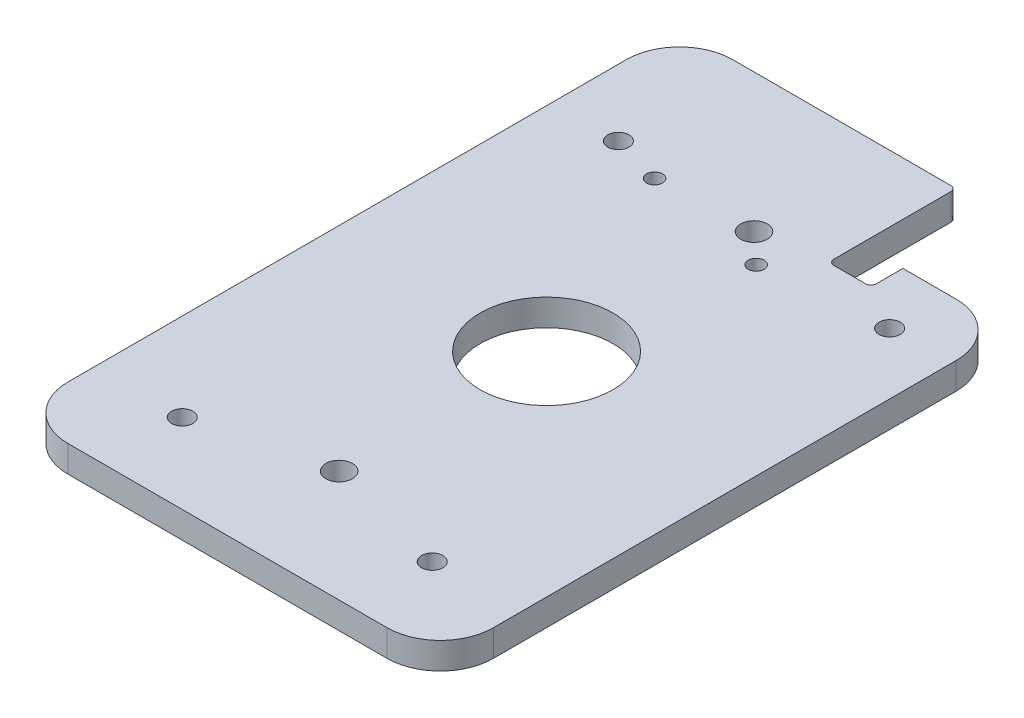
SolidWorks part; units mm, degrees
ref_plane "前视基准面" through (0, 0, 0) normal (0, 0, 1) x (1, 0, 0)
ref_plane "上视基准面" through (0, 0, 0) normal (0, 1, 0) x (1, 0, 0)
ref_plane "右视基准面" through (0, 0, 0) normal (1, 0, 0) x (0, 0, -1)
sketch "草图1" plane through (0, 0, 0) normal (0, 1, 0) x (1, 0, 0)
  line L0 (0, -49.286) -> (0, 59.6782) construction
  line L1 (-40, 65) -> (40, 65)
  line L2 (-40, 65) -> (-40, -60)
  line L3 (-40, -60) -> (40, -60)
  line L4 (40, 65) -> (40, -60)
  circle A0 centre (0, 0) radius 12.5
  dimension "D1" = 60
  dimension "D4" = 25
  dimension "D2" = 80
  dimension "D3" = 125
extrude "凸台-拉伸1" add sketch "草图1" along normal blind 5
sketch "草图2" plane through (0, 5, 0) normal (0, 1, 0) x (1, 0, 0)
  line L0 (40, 65) -> (-40, 65) construction
  line L1 (12, 65) -> (40, 65)
  line L2 (12, 65) -> (12, 47)
  line L3 (12, 47) -> (40, 47)
  line L4 (40, 65) -> (40, 47)
  line L5 (40, -60) -> (40, 65) construction
  dimension "D1" = 28
  dimension "D2" = 18
extrude "切除-拉伸1" cut sketch "草图2" against normal through all
hole_wizard "大小mm Clearance 暗销孔1" positions "草图3" profile "草图4" hole size "Ø4.0" standard "GB" end condition through all
sketch "草图3" plane through (0, 5, 0) normal (0, 1, 0) x (1, 0, 0)
  line L0 (0, -59.3844) -> (0, 58.2895) construction
  line L2 (30.3997, 0) -> (-33.5358, 0) construction
  point P0 (-23.5, -45)
  point P3 (23.5, -45)
  point P6 (28.5, 36)
  point P9 (-27.5, 41)
  dimension "D1" = 45
  dimension "D2" = 23.5
  dimension "D3" = 41
  dimension "D4" = 27.5
  dimension "D5" = 28.5
  dimension "D6" = 36
sketch "草图4" plane through (-23.5, 5, 45) normal (1, 0, 0) x (0, 0, 1)
  line L0 (0, 0) -> (0, 5)
  line L1 (0, 5) -> (2, 5)
  line L2 (2, 5) -> (2, 0)
  line L5 (2, 0) -> (0, 0)
  line L11 (0, -6.35) -> (0, 107.95) construction
  dimension "通孔孔直径" = 4
  dimension "通孔孔深度" = 5
hole_wizard "大小mm Transitional 暗销孔1" positions "草图5" profile "草图6" hole size "Ø5.0" standard "GB" end condition through all
sketch "草图5" plane through (0, 5, 0) normal (0, 1, 0) x (1, 0, 0)
  line L0 (28.4574, 0) -> (-29.0037, 0) construction
  line L1 (28.4574, 0) -> (-30.1367, 0) construction
  point P0 (0, -39)
  point P3 (0, 39)
  dimension "D1" = 39
sketch "草图6" plane through (0, 5, 39) normal (1, 0, 0) x (0, 0, 1)
  line L0 (0, 0) -> (0, 5)
  line L1 (0, 5) -> (2.5, 5)
  line L2 (2.5, 5) -> (2.5, 0)
  line L5 (2.5, 0) -> (0, 0)
  line L11 (0, -6.35) -> (0, 107.95) construction
  dimension "通孔孔直径" = 5
  dimension "通孔孔深度" = 5
fillet "圆角1" radius 10 4 edges at (40, 2.5, 60) (-40, 2.5, 60) (-40, 2.5, -65) (40, 2.5, -47)
hole_wizard "大小mm Transitional 暗销孔2" positions "草图9" profile "草图10" hole size "Ø3.0" standard "GB" end condition through all
sketch "草图9" plane through (0, 5, 0) normal (0, 1, 0) x (1, 0, 0)
  line L0 (0, 0) -> (0, 52.6631) construction
  line L2 (22.6815, 0) -> (-25.0677, 0) construction
  point P0 (5.6094, 33.8)
  point P3 (-18, 38.3)
  point P15 (0, 0)
  point P16 (0, 0)
  point P17 (5.6094, 33.8)
  point P19 (0, 0)
  dimension "D1" = 33.8
  dimension "D2" = 18
  dimension "D3" = 5.6094
  dimension "D4" = 38.3
sketch "草图10" plane through (5.6094, 5, -33.8) normal (1, 0, 0) x (0, 0, 1)
  line L0 (0, 0) -> (0, 5)
  line L1 (0, 5) -> (1.5, 5)
  line L2 (1.5, 5) -> (1.5, 0)
  line L5 (1.5, 0) -> (0, 0)
  line L11 (0, -6.35) -> (0, 107.95) construction
  dimension "通孔孔直径" = 3
  dimension "通孔孔深度" = 5
sketch "草图12" plane through (0, 5, 0) normal (0, 1, 0) x (1, 0, 0)
  line L1 (12, 47) -> (20, 47)
  line L2 (12, 47) -> (12, 41)
  line L3 (12, 41) -> (20, 41)
  line L4 (20, 47) -> (20, 41)
  dimension "D1" = 6
  dimension "D2" = 8
extrude "切除-拉伸2" cut sketch "草图12" against normal through all
fillet "圆角2" radius 1 3 edges at (20, 2.5, -41) (12, 2.5, -41) (12, 2.5, -65)
